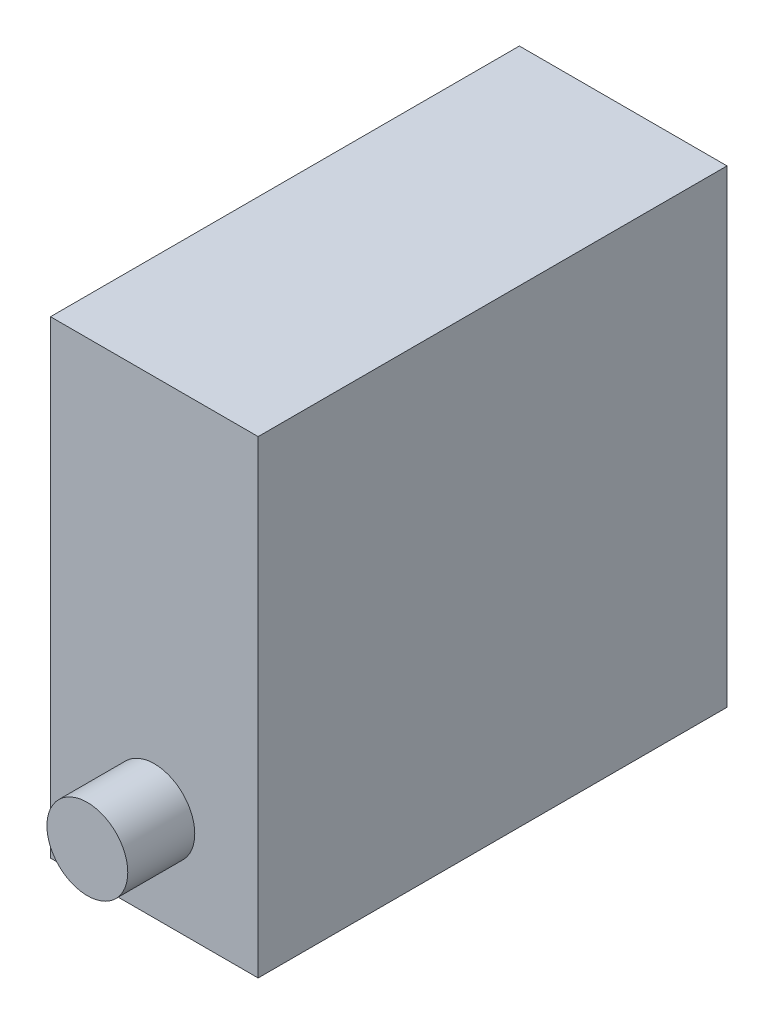
SolidWorks part; units mm, degrees
ref_plane "Front Plane" through (0, 0, 0) normal (0, 0, 1) x (1, 0, 0)
ref_plane "Top Plane" through (0, 0, 0) normal (0, 1, 0) x (1, 0, 0)
ref_plane "Right Plane" through (0, 0, 0) normal (1, 0, 0) x (0, 0, -1)
sketch "Sketch1" plane through (0, 0, 0) normal (0, 0, 1) x (1, 0, 0)
  line L1 (0, 0) -> (6.2, 0)
  line L2 (0, 0) -> (0, -14)
  line L3 (0, -14) -> (6.2, -14)
  line L4 (6.2, 0) -> (6.2, -14)
  dimension "D1" = 6.2
  dimension "D2" = 14
extrude "Boss-Extrude1" add sketch "Sketch1" along normal blind 14
ref_plane "Plane1" through (6.2, -14, 14) normal (0, 0, -1) x (-1, 0, 0)
sketch "Sketch3" plane through (0, 0, 14) normal (0, 0, 1) x (1, 0, 0)
  line L0 (0, -14) -> (6.2, -14) construction
  circle A0 centre (3.1, -11.216) radius 1.2073
  point P6 (3.1, -14)
extrude "Boss-Extrude2" add sketch "Sketch3" along normal blind 2
